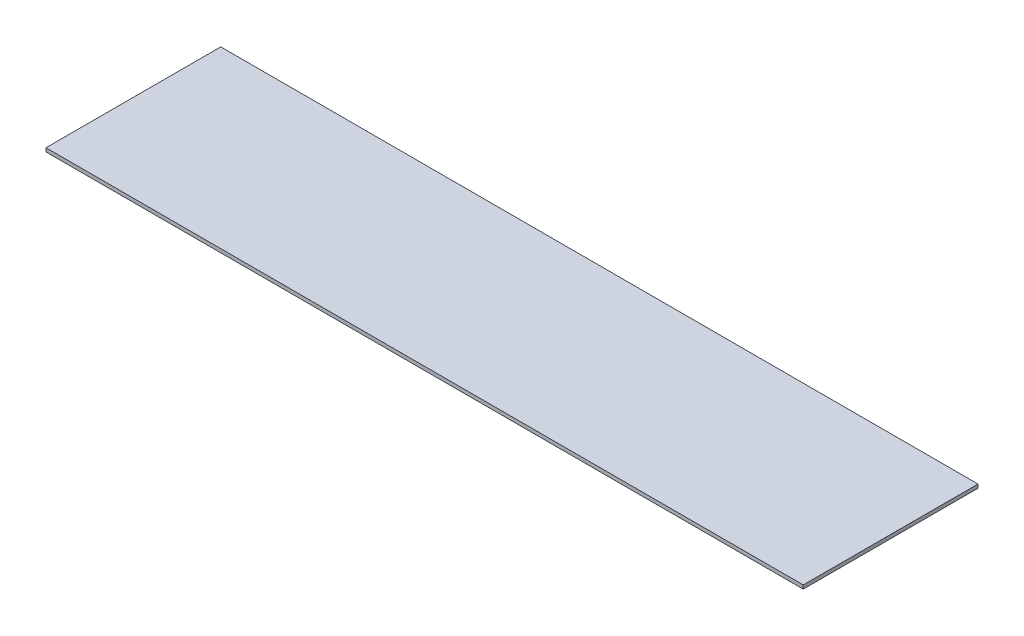
SolidWorks part; units mm, degrees
ref_plane "Alzado" through (0, 0, 0) normal (0, 0, 1) x (1, 0, 0)
ref_plane "Planta" through (0, 0, 0) normal (0, 1, 0) x (1, 0, 0)
ref_plane "Vista lateral" through (0, 0, 0) normal (1, 0, 0) x (0, 0, -1)
sketch "Croquis1" plane through (0, 0, 0) normal (0, 1, 0) x (1, 0, 0)
  line L1 (-208, 48) -> (208, 48)
  line L2 (-208, 48) -> (-208, -48)
  line L3 (-208, -48) -> (208, -48)
  line L4 (208, 48) -> (208, -48)
  line L5 (-208, 48) -> (208, -48) construction
  line L6 (-208, -48) -> (208, 48) construction
  point P0 (0, 0)
extrude "Saliente-Extruir1" add sketch "Croquis1" along normal blind 2
